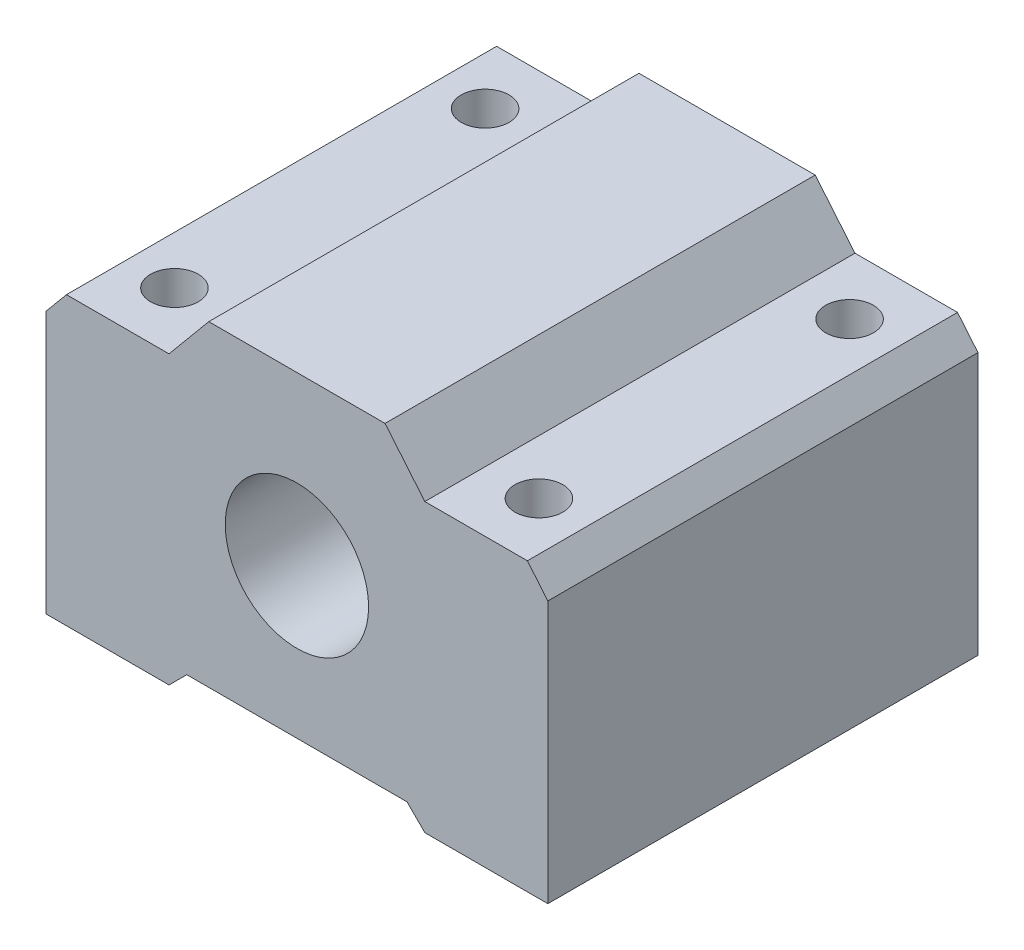
SolidWorks part; units mm, degrees
ref_plane "Front Plane" through (0, 0, 0) normal (0, 0, 1) x (1, 0, 0)
ref_plane "Top Plane" through (0, 0, 0) normal (0, 1, 0) x (1, 0, 0)
ref_plane "Right Plane" through (0, 0, 0) normal (1, 0, 0) x (0, 0, -1)
sketch "Sketch1" plane through (0, 0, 0) normal (0, 0, 1) x (1, 0, 0)
  line L0 (-7.3763, 14) -> (-10.7049, 10)
  line L1 (-21, -14) -> (-12.1932, -14)
  line L2 (-21, -14) -> (-21, 7.9417)
  line L3 (-7.3763, 14) -> (7.3763, 14)
  line L4 (21, -14) -> (21, 7.9417)
  line L5 (12.1932, -14) -> (21, -14)
  line L7 (-10.7049, 10) -> (-19.2872, 10)
  line L8 (-19.2872, 10) -> (-21, 7.9417)
  line L9 (0, 14) -> (0, -14) construction
  line L10 (7.3763, 14) -> (10.7049, 10)
  line L11 (10.7049, 10) -> (19.2872, 10)
  line L12 (19.2872, 10) -> (21, 7.9417)
  line L13 (-12.1932, -14) -> (-10.7049, -14)
  line L14 (-9.2165, -12.5117) -> (9.2165, -12.5117)
  line L15 (-10.7049, -14) -> (-9.2165, -12.5117)
  line L17 (12.1932, -14) -> (10.7049, -14)
  line L18 (10.7049, -14) -> (9.2165, -12.5117)
  circle A0 centre (0, 0) radius 6
  point P0 (0, 0)
  dimension "D3" = 24
  dimension "D1" = 42
  dimension "D2" = 28
  dimension "D4" = 8.5824
  dimension "D5" = 8.5824
  dimension "D6" = 14.7527
  dimension "D7" = 18.4331
extrude "Boss-Extrude1" add sketch "Sketch1" along normal blind 36
sketch "Sketch2" plane through (0, -14, 0) normal (0, -1, 0) x (1, 0, 0)
  line L0 (0, 36) -> (0, 0) construction
  line L1 (-9.2165, 36) -> (9.2165, 36) construction
  line L2 (0, 18) -> (-21, 18) construction
  line L3 (-21, 36) -> (-21, 0) construction
  line L5 (-15.25, 5) -> (15.25, 5) construction
  line L6 (-15.25, 5) -> (-15.25, 31) construction
  line L7 (-15.25, 31) -> (15.25, 31) construction
  line L8 (15.25, 5) -> (15.25, 31) construction
  line L9 (-15.25, 5) -> (15.25, 31) construction
  line L10 (-15.25, 31) -> (15.25, 5) construction
  circle A0 centre (-15.25, 31) radius 2
  circle A1 centre (15.25, 31) radius 2
  circle A2 centre (15.25, 5) radius 2
  circle A3 centre (-15.25, 5) radius 2
  dimension "D1" = 30.5
  dimension "D2" = 26
extrude "Cut-Extrude1" cut sketch "Sketch2" against normal up to next
